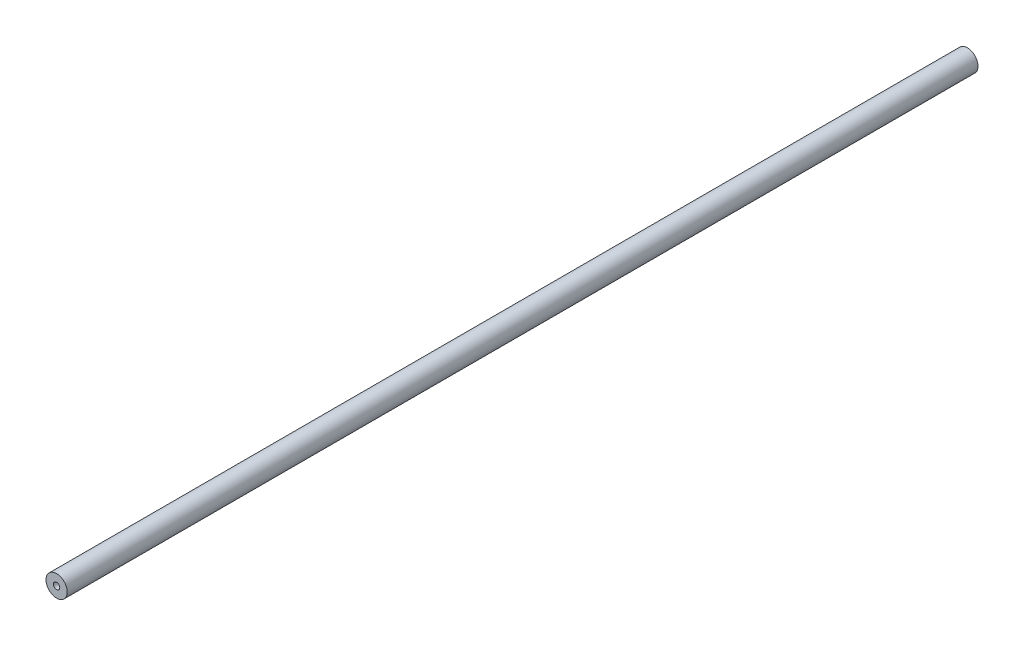
SolidWorks part; units mm, degrees
material "6061-T6 (SS)"
ref_plane "Front Plane" through (0, 0, 0) normal (0, 0, 1) x (1, 0, 0)
ref_plane "Top Plane" through (0, 0, 0) normal (0, 1, 0) x (1, 0, 0)
ref_plane "Right Plane" through (0, 0, 0) normal (1, 0, 0) x (0, 0, -1)
sketch "Sketch1" plane through (0, 0, 0) normal (0, 0, 1) x (1, 0, 0)
  circle A0 centre (0, 0) radius 6.4
  dimension "D1" = 12.8
extrude "Boss-Extrude1" add sketch "Sketch1" along normal blind 548.24
hole_wizard "#10-24 Tapped Hole1" positions "Sketch2" profile "Sketch3" tap size "#10-24" standard "ANSI Inch"
sketch "Sketch2" plane through (0, 0, 0) normal (0, 0, -1) x (-1, 0, 0)
  point P0 (0, 0)
sketch "Sketch3" plane through (0, 0, 0) normal (1, 0, 0) x (0, 1, 0)
  line L0 (0, 0) -> (0, 13.9708)
  line L1 (0, 13.9708) -> (1.8986, 12.83)
  line L2 (1.8986, 12.83) -> (1.8986, 0)
  line L5 (1.8986, 0) -> (0, 0)
  line L10 (0, 13.9708) -> (-1.8987, 12.83) construction
  line L11 (0, -6.35) -> (0, 107.95) construction
  dimension "Tap Drill Dia." = 3.7973
  dimension "Tap Drill Depth" = 12.83
  dimension "Drill Angle" = 118
hole_wizard "#10-24 Tapped Hole2" positions "Sketch4" profile "Sketch5" tap size "#10-24" standard "ANSI Inch"
sketch "Sketch4" plane through (0, 0, 548.24) normal (0, 0, 1) x (1, 0, 0)
  point P0 (0, 0)
sketch "Sketch5" plane through (0, 0, 548.24) normal (1, 0, 0) x (0, -1, 0)
  line L0 (0, 0) -> (0, 13.9708)
  line L1 (0, 13.9708) -> (1.8986, 12.83)
  line L2 (1.8986, 12.83) -> (1.8986, 0)
  line L5 (1.8986, 0) -> (0, 0)
  line L10 (0, 13.9708) -> (-1.8987, 12.83) construction
  line L11 (0, -6.35) -> (0, 107.95) construction
  dimension "Tap Drill Dia." = 3.7973
  dimension "Tap Drill Depth" = 12.83
  dimension "Drill Angle" = 118
